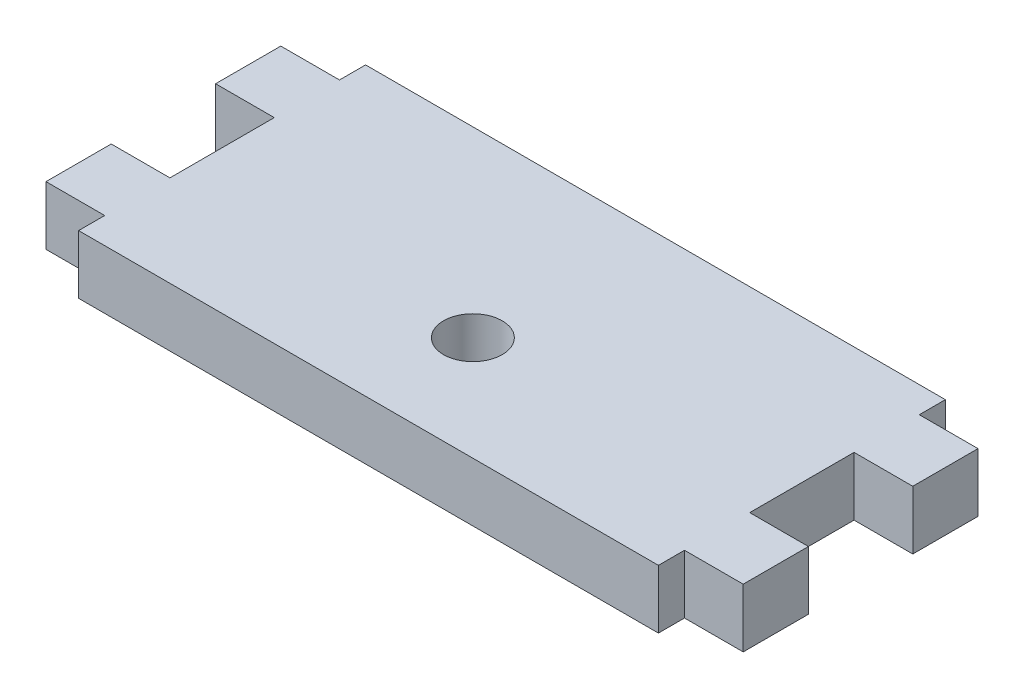
SolidWorks part; units mm, degrees
ref_plane "Front Plane" through (0, 0, 0) normal (0, 0, 1) x (1, 0, 0)
ref_plane "Top Plane" through (0, 0, 0) normal (0, 1, 0) x (1, 0, 0)
ref_plane "Right Plane" through (0, 0, 0) normal (1, 0, 0) x (0, 0, -1)
sketch "Sketch1" plane through (0, 0, 0) normal (0, 1, 0) x (1, 0, 0)
  line L0 (-22.225, -9) -> (-22.225, -11)
  line L1 (-22.225, 11) -> (0, 11)
  line L2 (-22.225, 11) -> (-22.225, 9)
  line L3 (-22.225, -11) -> (0, -11)
  line L4 (0, 11) -> (0, -11)
  line L5 (-22.225, -9) -> (-26.725, -9)
  line L6 (-22.225, 4) -> (-22.225, -4)
  line L7 (-22.225, -4) -> (-26.725, -4)
  line L8 (-26.725, -9) -> (-26.725, -4)
  line L9 (-22.225, 4) -> (-26.725, 4)
  line L11 (-22.225, 9) -> (-26.725, 9)
  line L12 (-26.725, 4) -> (-26.725, 9)
  dimension "D1" = 22.225
  dimension "D2" = 22
  dimension "D3" = 2
  dimension "D4" = 5
  dimension "D5" = 4.5
extrude "Boss-Extrude1" add sketch "Sketch1" along normal blind 4.5
mirror "Mirror1" about plane through (0, 4.5, -11) normal (-1, 0, 0) of "Boss-Extrude1"
sketch "Sketch2" plane through (0, 4.5, 0) normal (0, 1, 0) x (1, 0, 0)
  circle A0 centre (0, -3) radius 2.25
  dimension "D1" = 4.5
  dimension "D2" = 3
extrude "Cut-Extrude1" cut sketch "Sketch2" against normal through all
